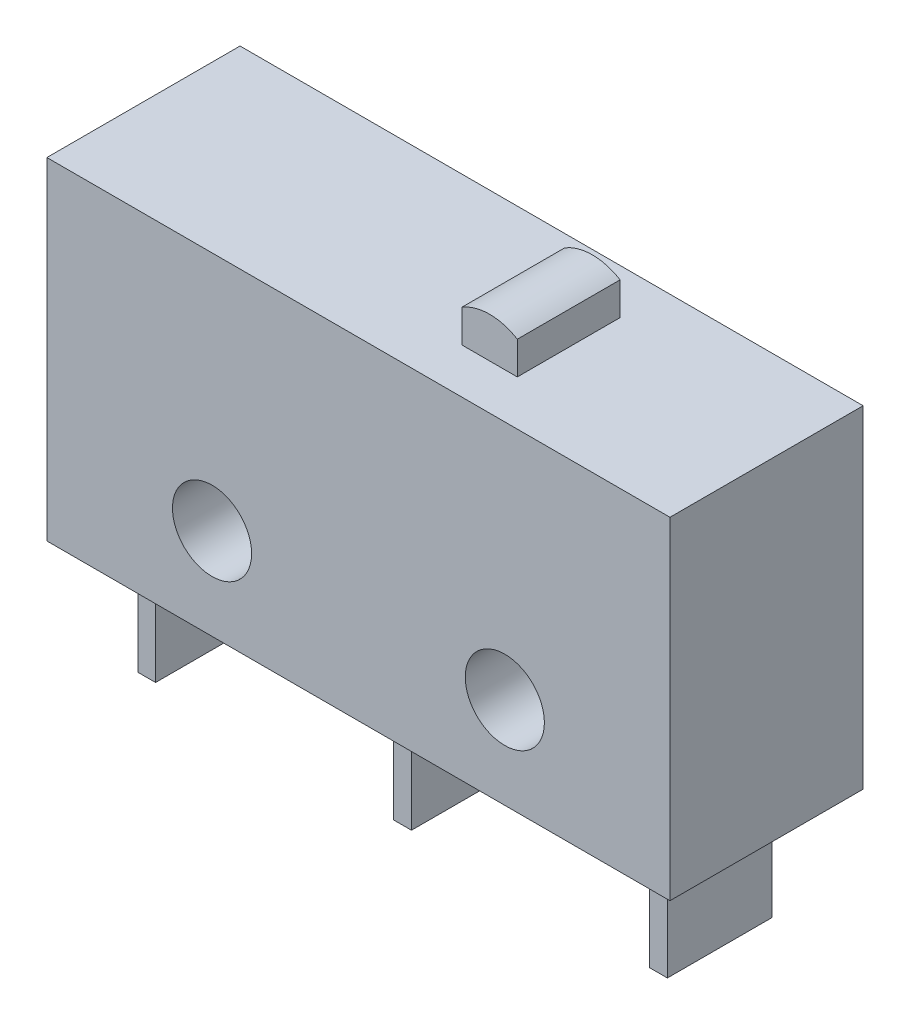
SolidWorks part; units mm, degrees
ref_plane "Front Plane" through (0, 0, 0) normal (0, 0, 1) x (1, 0, 0)
ref_plane "Top Plane" through (0, 0, 0) normal (0, 1, 0) x (1, 0, 0)
ref_plane "Right Plane" through (0, 0, 0) normal (1, 0, 0) x (0, 0, -1)
sketch "Sketch1" plane through (0, 0, 0) normal (0, 0, 1) x (1, 0, 0)
  line L1 (10, 10.66) -> (-10, 10.66)
  line L2 (10, 10.66) -> (10, 0)
  line L3 (10, 0) -> (-10, 0)
  line L4 (-10, 10.66) -> (-10, 0)
  line L5 (0, 0) -> (0, 10.66) construction
  line L6 (10, 5.33) -> (-10, 5.33) construction
  point P0 (0, 5.33)
  point P4 (0, 0)
  dimension "D1" = 20
  dimension "D2" = 10.66
extrude "Boss-Extrude1" add sketch "Sketch1" along normal mid plane 6.2
sketch "Sketch2" plane through (0, 0, 3.1) normal (0, 0, 1) x (1, 0, 0)
  line L0 (-4.699, 2.9337) -> (4.699, 2.9337) construction
  line L1 (0, 2.9337) -> (0, 0) construction
  line L2 (-10, 0) -> (10, 0) construction
  circle A0 centre (4.699, 2.9337) radius 1.27
  circle A1 centre (-4.699, 2.9337) radius 1.27
  dimension "D2" = 2.54
  dimension "D3" = 1.6637
  dimension "D1" = 9.398
extrude "Cut-Extrude1" cut sketch "Sketch2" against normal through all
sketch "Sketch3" plane through (0, 0, 0) normal (0, -1, 0) x (1, 0, 0)
  line L0 (-8.2142, 0) -> (8.2142, 0) construction
  line L2 (-7.9285, 1.6827) -> (-8.5, 1.6827)
  line L3 (-7.9285, 1.6827) -> (-7.9285, -1.6827)
  line L4 (-7.9285, -1.6827) -> (-8.5, -1.6827)
  line L5 (-8.5, 1.6827) -> (-8.5, -1.6827)
  line L6 (-8.2143, -1.6827) -> (-8.2143, 1.6827) construction
  line L7 (-7.9285, 0) -> (-8.5, 0) construction
  line L8 (0.2857, 1.6827) -> (-0.2858, 1.6827)
  line L9 (0.2857, 1.6827) -> (0.2858, -1.6827)
  line L10 (0.2858, -1.6827) -> (-0.2858, -1.6827)
  line L11 (-0.2858, 1.6827) -> (-0.2858, -1.6827)
  line L12 (0, -1.6827) -> (0, 1.6827) construction
  line L13 (0.2857, 0) -> (-0.2857, 0) construction
  line L14 (8.5, 1.6827) -> (7.9285, 1.6827)
  line L15 (8.5, 1.6827) -> (8.5, -1.6827)
  line L16 (8.5, -1.6827) -> (7.9285, -1.6827)
  line L17 (7.9285, 1.6827) -> (7.9285, -1.6827)
  line L18 (8.2143, -1.6827) -> (8.2143, 1.6827) construction
  line L19 (8.5, 0) -> (7.9285, 0) construction
  point P6 (0, 0)
  dimension "D1" = 0.5715
  dimension "D2" = 17
  dimension "D3" = 3.3655
extrude "Boss-Extrude2" add sketch "Sketch3" along normal blind 3.6068
sketch "Sketch4" plane through (0, 10.66, 0) normal (0, 1, 0) x (1, 0, 0)
  line L0 (10, -3.1) -> (10, 3.1) construction
  line L1 (3.65, -1.65) -> (1.872, -1.65)
  line L2 (3.65, -1.65) -> (3.65, 1.65)
  line L3 (3.65, 1.65) -> (1.872, 1.65)
  line L4 (1.872, -1.65) -> (1.872, 1.65)
  line L5 (2.761, 1.65) -> (2.761, -1.65) construction
  line L6 (3.65, 0) -> (1.872, 0) construction
  point P112 (2.761, 0)
  dimension "D1" = 1.778
  dimension "D2" = 6.35
  dimension "D3" = 3.3
extrude "Boss-Extrude3" add sketch "Sketch4" along normal blind 1.3
sketch "Sketch5" plane through (0, 0, 1.65) normal (0, 0, 1) x (1, 0, 0)
  line L0 (1.872, 11.71) -> (3.65, 11.71) construction
  line L4 (1.872, 10.66) -> (3.65, 10.66)
  line L5 (3.65, 10.66) -> (3.65, 11.96)
  line L6 (3.65, 11.96) -> (1.872, 11.96)
  line L7 (1.872, 11.96) -> (1.872, 10.66)
  line L8 (1.872, 10.66) -> (3.65, 10.66)
  line L9 (3.65, 10.66) -> (3.65, 11.96)
  line L10 (3.65, 11.96) -> (1.872, 11.96)
  line L11 (1.872, 11.96) -> (1.872, 10.66)
  arc A0 (1.872, 11.71) -> (3.65, 11.71) centre (2.761, 10.2544) cw
  line M8 (3.65, 11.96) -> (1.872, 11.96)
  line M9 (1.872, 11.96) -> (1.872, 10.66)
  dimension "D2" = 0.25
  dimension "D1" = 0
extrude "Cut-Extrude2" cut sketch "Sketch5" against normal through all contours A0 L10 M9 | A0 L9 M8
